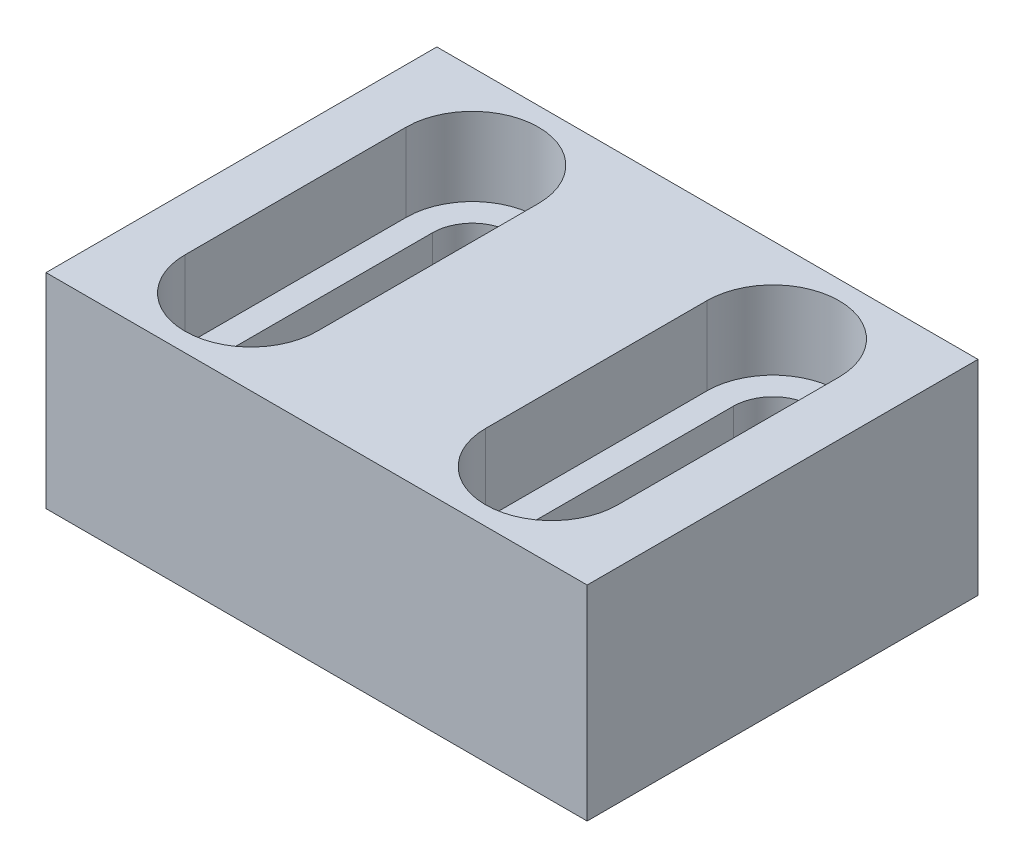
SolidWorks part; units mm, degrees
ref_plane "Front Plane" through (0, 0, 0) normal (0, 0, 1) x (1, 0, 0)
ref_plane "Top Plane" through (0, 0, 0) normal (0, 1, 0) x (1, 0, 0)
ref_plane "Right Plane" through (0, 0, 0) normal (1, 0, 0) x (0, 0, -1)
sketch "Sketch1" plane through (0, 0, 0) normal (0, 1, 0) x (1, 0, 0)
  line L0 (-12.5, -9.2) -> (-12.5, 9.2) construction
  line L1 (-22.5, -16.25) -> (22.5, -16.25)
  line L2 (-22.5, -16.25) -> (-22.5, 16.25)
  line L3 (-22.5, 16.25) -> (22.5, 16.25)
  line L4 (22.5, -16.25) -> (22.5, 16.25)
  line L5 (-22.5, -16.25) -> (22.5, 16.25) construction
  line L6 (-22.5, 16.25) -> (22.5, -16.25) construction
  line L7 (-15.8, -9.2) -> (-15.8, 9.2)
  line L8 (-9.2, -9.2) -> (-9.2, 9.2)
  line L9 (12.5, -9.2) -> (12.5, 9.2) construction
  line L10 (9.2, -9.2) -> (9.2, 9.2)
  line L11 (15.8, -9.2) -> (15.8, 9.2)
  arc A0 (-15.8, -9.2) -> (-9.2, -9.2) centre (-12.5, -9.2) ccw
  arc A1 (-9.2, 9.2) -> (-15.8, 9.2) centre (-12.5, 9.2) ccw
  arc A2 (9.2, -9.2) -> (15.8, -9.2) centre (12.5, -9.2) ccw
  arc A3 (15.8, 9.2) -> (9.2, 9.2) centre (12.5, 9.2) ccw
  point P0 (0, 0)
  point P8 (-12.5, 0)
  point P14 (12.5, 0)
  point P20 (0, 0)
  dimension "D1" = 45
  dimension "D2" = 32.5
  dimension "D3" = 6.6
  dimension "D4" = 18.4
  dimension "D5" = 12.5
  dimension "D6" = 12.5
extrude "Boss-Extrude1" add sketch "Sketch1" along normal blind 17
sketch "Sketch2" plane through (0, 17, 0) normal (0, 1, 0) x (1, 0, 0)
  line L0 (15.8, -9.2) -> (15.8, 9.2) construction
  line L1 (9.2, 9.2) -> (9.2, -9.2) construction
  line L2 (-9.2, -9.2) -> (-9.2, 9.2) construction
  line L3 (-15.8, 9.2) -> (-15.8, -9.2) construction
  line L4 (15.8, -9.2) -> (15.8, 9.2) construction
  line L5 (9.2, 9.2) -> (9.2, -9.2) construction
  line L6 (-9.2, -9.2) -> (-9.2, 9.2) construction
  line L7 (-15.8, 9.2) -> (-15.8, -9.2) construction
  line L8 (18, -9.2) -> (18, 9.2)
  line L9 (7, 9.2) -> (7, -9.2)
  line L10 (-7, -9.2) -> (-7, 9.2)
  line L11 (-18, 9.2) -> (-18, -9.2)
  arc A0 (9.2, -9.2) -> (15.8, -9.2) centre (12.5, -9.2) ccw construction
  arc A1 (15.8, 9.2) -> (9.2, 9.2) centre (12.5, 9.2) ccw construction
  arc A2 (-15.8, -9.2) -> (-9.2, -9.2) centre (-12.5, -9.2) ccw construction
  arc A3 (-9.2, 9.2) -> (-15.8, 9.2) centre (-12.5, 9.2) ccw construction
  arc A4 (9.2, -9.2) -> (15.8, -9.2) centre (12.5, -9.2) ccw construction
  arc A5 (15.8, 9.2) -> (9.2, 9.2) centre (12.5, 9.2) ccw construction
  arc A6 (-15.8, -9.2) -> (-9.2, -9.2) centre (-12.5, -9.2) ccw construction
  arc A7 (-9.2, 9.2) -> (-15.8, 9.2) centre (-12.5, 9.2) ccw construction
  arc A8 (18, 9.2) -> (7, 9.2) centre (12.5, 9.2) ccw
  arc A9 (7, -9.2) -> (18, -9.2) centre (12.5, -9.2) ccw
  arc A10 (-7, 9.2) -> (-18, 9.2) centre (-12.5, 9.2) ccw
  arc A11 (-18, -9.2) -> (-7, -9.2) centre (-12.5, -9.2) ccw
  dimension "D1" = 2.2
extrude "Cut-Extrude1" cut sketch "Sketch2" against normal blind 6.5
hole_wizard "M3 Tapped Hole1" positions "Sketch3" profile "Sketch4" tap size "M3" standard "DIN"
sketch "Sketch3" plane through (0, 0, -16.25) normal (0, 0, -1) x (-1, 0, 0)
  line L0 (-22.5, 0) -> (22.5, 0) construction
  line L1 (-22.5, 17) -> (22.5, 17) construction
  point P0 (-18.5, 5)
  point P2 (0, 12)
  point P4 (18.5, 5)
  dimension "D1" = 5
  dimension "D2" = 5
  dimension "D3" = 18.5
  dimension "D4" = 18.5
sketch "Sketch4" plane through (18.5, 5, -16.25) normal (1, 0, 0) x (0, 1, 0)
  line L0 (0, 0) -> (0, 10.7511)
  line L1 (0, 10.7511) -> (1.25, 10)
  line L2 (1.25, 10) -> (1.25, 0)
  line L5 (1.25, 0) -> (0, 0)
  line L10 (0, 10.7511) -> (-1.25, 10) construction
  line L11 (0, -6.35) -> (0, 107.95) construction
  dimension "Tap Drill Dia." = 2.5
  dimension "Tap Drill Depth" = 10
  dimension "Drill Angle" = 118
cosmetic thread "Hole Thread1" parameters "D1"=6, "D2"=3
cosmetic thread "Hole Thread2" parameters "D1"=6, "D2"=3
cosmetic thread "Hole Thread3" parameters "D1"=6, "D2"=3
equation "\"`17\"=10"
